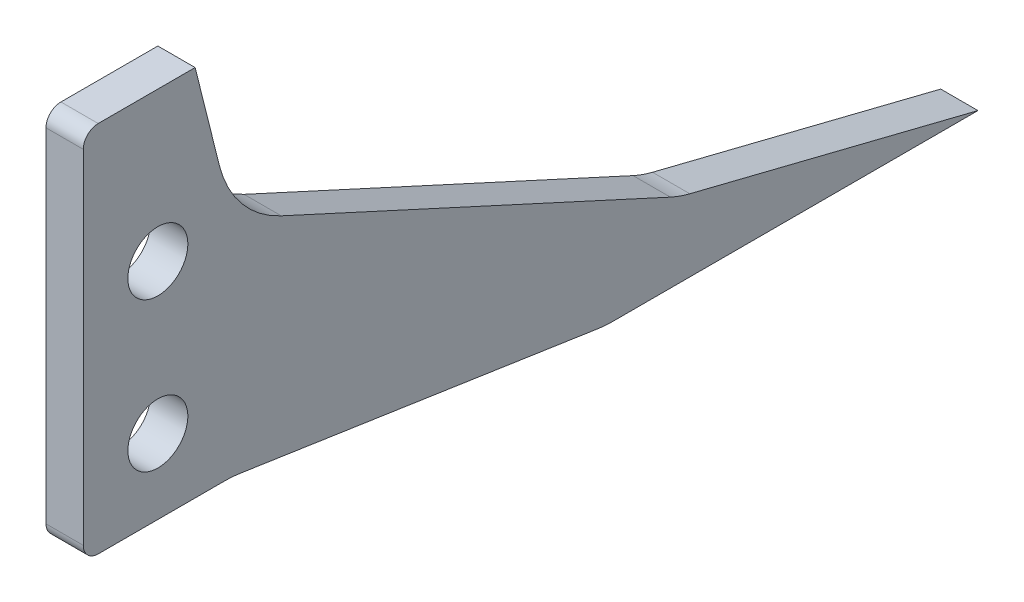
SolidWorks part; units mm, degrees
material "PLA/ABS"
ref_plane "Front Plane" through (0, 0, 0) normal (0, 0, 1) x (1, 0, 0)
ref_plane "Top Plane" through (0, 0, 0) normal (0, 1, 0) x (1, 0, 0)
ref_plane "Right Plane" through (0, 0, 0) normal (1, 0, 0) x (0, 0, -1)
other "Center of Mass"
other "Bounding Box"
ref_plane "Default Plane" through (-8.9266, -12.7485, 0) normal (-0.1736, 0.9848, 0) x (0.9848, 0.1736, 0)
sketch "Sketch1" plane through (0, 0, 0) normal (0, 1, 0) x (1, 0, 0)
  line L0 (0, 0) -> (0, -50.8) construction
  line L1 (0, -50.8) -> (-6.35, -50.8) construction
  line L2 (-63.5, -50.8) -> (-57.15, -50.8) construction
  line L3 (-57.15, -60.7695) -> (-6.35, -60.7695)
  line L4 (-57.15, -60.7695) -> (-57.15, -40.8305)
  line L5 (-57.15, -40.8305) -> (-6.35, -40.8305)
  line L6 (-6.35, -60.7695) -> (-6.35, -40.8305)
  line L7 (-57.15, -60.7695) -> (-6.35, -40.8305) construction
  line L8 (-57.15, -40.8305) -> (-6.35, -60.7695) construction
  line L9 (-73.66, -71.4375) -> (-63.5, -71.4375)
  line L10 (-73.66, -71.4375) -> (-73.66, -30.1625)
  line L11 (-73.66, -30.1625) -> (-63.5, -30.1625)
  line L12 (-63.5, -71.4375) -> (-63.5, -30.1625)
  line L13 (-73.66, -71.4375) -> (-63.5, -30.1625) construction
  line L14 (-73.66, -30.1625) -> (-63.5, -71.4375) construction
  line L15 (57.15, -40.8305) -> (6.35, -40.8305)
  line L16 (-47.625, -82.55) -> (9.525, -82.55)
  line L17 (-47.625, -82.55) -> (-47.625, -66.04)
  line L18 (-47.625, -66.04) -> (9.525, -66.04)
  line L19 (9.525, -82.55) -> (9.525, -66.04)
  line L20 (-47.625, -82.55) -> (9.525, -66.04) construction
  line L21 (-47.625, -66.04) -> (9.525, -82.55) construction
  line L22 (6.35, -60.7695) -> (6.35, -40.8305)
  line L23 (57.15, -60.7695) -> (6.35, -60.7695)
  line L24 (57.15, -60.7695) -> (57.15, -40.8305)
  line L25 (73.66, -30.1625) -> (63.5, -30.1625)
  line L26 (63.5, -71.4375) -> (63.5, -30.1625)
  line L27 (73.66, -71.4375) -> (63.5, -71.4375)
  line L28 (73.66, -71.4375) -> (73.66, -30.1625)
  line L30 (47.625, -82.55) -> (4.445, -82.55)
  line L31 (47.625, -82.55) -> (47.625, -62.4078)
  line L32 (47.625, -62.4078) -> (4.445, -62.4078)
  line L33 (4.445, -82.55) -> (4.445, -62.4078)
  line L34 (47.625, -82.55) -> (4.445, -62.4078) construction
  line L35 (47.625, -62.4078) -> (4.445, -82.55) construction
  line L36 (-57.15, -88.9) -> (57.15, -88.9)
  line L37 (-57.15, -88.9) -> (-57.15, 0)
  line L38 (-57.15, 0) -> (57.15, 0)
  line L39 (57.15, -88.9) -> (57.15, 0)
  line L40 (-57.15, -88.9) -> (57.15, 0) construction
  line L41 (-57.15, 0) -> (57.15, -88.9) construction
  point P3 (-19.05, -74.295)
  point P6 (-31.75, -50.8)
  point P12 (-68.58, -50.8)
  point P22 (0, 0)
  point P23 (0, -44.45)
  point P36 (0, 6.35)
  point P38 (26.035, -72.4789)
  dimension "D2" = 50.8
  dimension "D3" = 19.939
  dimension "D4" = 41.275
  dimension "D5" = 10.16
  dimension "D6" = 57.15
  dimension "D7" = 16.51
  dimension "D8" = 43.18
  dimension "D9" = 20.1422
  dimension "D10" = 6.35
  dimension "D11" = 114.3
  dimension "D12" = 38.1
  dimension "D13" = 6.35
  dimension "D14" = 9.525
  dimension "D15" = 6.35
  dimension "D16" = 9.525
  dimension "D17" = 88.9
  dimension "D18" = 6.35
sketch "Sketch2" plane through (0, 0, 0) normal (1, 0, 0) x (0, 0, -1)
  line L1 (-88.9, 12.7) -> (0, 12.7)
  line L2 (-88.9, 12.7) -> (-88.9, -12.7)
  line L3 (-88.9, -12.7) -> (0, -12.7)
  line L4 (0, 12.7) -> (0, -12.7)
  line L5 (-88.9, 12.7) -> (0, -12.7) construction
  line L6 (-88.9, -12.7) -> (0, 12.7) construction
  line L7 (-88.9, 12.7) -> (12.7, 12.7)
  line L8 (-88.9, 12.7) -> (-88.9, 15.875)
  line L9 (-88.9, 15.875) -> (12.7, 15.875)
  line L10 (12.7, 12.7) -> (12.7, 15.875)
  line L11 (-88.9, 12.7) -> (12.7, 15.875) construction
  line L12 (-88.9, 15.875) -> (12.7, 12.7) construction
  line L13 (-88.9, -12.7) -> (0, -12.7)
  line L14 (-88.9, -12.7) -> (-88.9, -15.875)
  line L15 (-88.9, -15.875) -> (0, -15.875)
  line L16 (0, -12.7) -> (0, -15.875)
  line L17 (-88.9, -12.7) -> (0, -15.875) construction
  line L18 (-88.9, -15.875) -> (0, -12.7) construction
  circle A0 centre (-50.8, 0) radius 20.6375
  point P4 (-71.4375, 0)
  point P5 (-44.45, 0)
  point P15 (-38.1, 14.2875)
  point P19 (-44.45, -14.2875)
  dimension "D1" = 25.4
  dimension "D2" = 3.175
  dimension "D3" = 12.7
sketch "Sketch3" plane through (0, 0, 0) normal (0, 1, 0) x (1, 0, 0)
  line L1 (-57.15, -88.9) -> (57.15, -88.9)
  line L2 (-57.15, -88.9) -> (-57.15, 0)
  line L3 (-57.15, 0) -> (57.15, 0)
  line L4 (57.15, -88.9) -> (57.15, 0)
  line L5 (-57.15, -88.9) -> (57.15, 0) construction
  line L6 (-57.15, 0) -> (57.15, -88.9) construction
  line L7 (-47.625, -6.35) -> (47.625, -6.35)
  line L8 (-47.625, -6.35) -> (-47.625, -82.55)
  line L9 (-47.625, -82.55) -> (47.625, -82.55)
  line L10 (47.625, -6.35) -> (47.625, -82.55)
  line L11 (-47.625, -6.35) -> (47.625, -82.55) construction
  line L12 (-47.625, -82.55) -> (47.625, -6.35) construction
  point P0 (0, -44.45)
  point P7 (0, -44.45)
extrude "Boss-Extrude1" add sketch "Sketch3" along normal up to vertex (12.7 mm away) and the other way up to vertex (12.7 mm away) up to point (0, 12.7, 88.9) other way up to point (0, -12.7, 88.9)
sketch "Sketch4" plane through (0, -12.7, 0) normal (0, -1, 0) x (1, 0, 0)
  line L1 (-57.15, 88.9) -> (57.15, 88.9)
  line L2 (-57.15, 88.9) -> (-57.15, 0)
  line L3 (-57.15, 0) -> (57.15, 0)
  line L4 (57.15, 88.9) -> (57.15, 0)
  line L5 (-57.15, 88.9) -> (57.15, 0) construction
  line L6 (-57.15, 0) -> (57.15, 88.9) construction
  point P0 (0, 44.45)
extrude "Boss-Extrude2" add sketch "Sketch4" along normal up to vertex (3.175 mm away) up to point (0, -15.875, 88.9)
sketch "Sketch5" plane through (0, 12.7, 0) normal (0, 1, 0) x (1, 0, 0)
  line L1 (-57.15, 0) -> (-57.15, -88.9)
  line L2 (-57.15, -88.9) -> (57.15, -88.9)
  line L3 (57.15, -88.9) -> (57.15, 0)
  line L5 (-57.15, 0) -> (57.15, 0)
extrude "Boss-Extrude3" add sketch "Sketch5" along normal up to vertex (3.175 mm away) separate body up to point (0, 15.875, 88.9)
sketch "Sketch7" plane through (0, -12.7, 0) normal (0, 1, 0) x (1, 0, 0)
  line L0 (-6.35, -60.7695) -> (-6.35, -40.8305) construction
  line L1 (-47.625, -38.1) -> (-6.35, -38.1)
  line L2 (-47.625, -38.1) -> (-47.625, -63.5)
  line L3 (-47.625, -63.5) -> (-6.35, -63.5)
  line L4 (-6.35, -38.1) -> (-6.35, -63.5)
  line L5 (-47.625, -38.1) -> (-6.35, -63.5) construction
  line L6 (-47.625, -63.5) -> (-6.35, -38.1) construction
  line L7 (47.625, -38.1) -> (6.35, -38.1)
  line L8 (47.625, -38.1) -> (47.625, -63.5)
  line L9 (47.625, -63.5) -> (6.35, -63.5)
  line L10 (6.35, -38.1) -> (6.35, -63.5)
  line L11 (47.625, -38.1) -> (6.35, -63.5) construction
  line L12 (47.625, -63.5) -> (6.35, -38.1) construction
  line L13 (6.35, -60.7695) -> (6.35, -40.8305) construction
  line L14 (0, -50.8) -> (-6.35, -50.8) construction
  line L15 (47.625, -82.55) -> (47.625, -6.35) construction
  line L16 (-47.625, -6.35) -> (-47.625, -82.55) construction
  point P4 (-26.9875, -50.8)
  point P10 (26.9875, -50.8)
  dimension "D1" = 25.4
extrude "Boss-Extrude4" add sketch "Sketch7" along normal blind 6.35
sketch "Sketch6" plane through (-57.15, 0, 0) normal (-1, 0, 0) x (0, 0, 1)
  circle A0 centre (50.8, 0) radius 9.9695
extrude "Cut-Extrude1" cut sketch "Sketch6" against normal through all
ref_plane "Plane1" through (0, 0, 0) normal (1, 0, 0) x (0, 0, -1)
sketch "Sketch13" plane through (0, -12.7, 0) normal (0, 1, 0) x (1, 0, 0)
  line L0 (-47.625, -63.5) -> (-6.35, -63.5) construction
  line L1 (-6.35, -38.1) -> (-32.385, -38.1)
  line L2 (-6.35, -38.1) -> (-6.35, -63.5)
  line L3 (-6.35, -63.5) -> (-32.385, -63.5)
  line L4 (-32.385, -38.1) -> (-32.385, -63.5)
  line L5 (-6.35, -38.1) -> (-32.385, -63.5) construction
  line L6 (-6.35, -63.5) -> (-32.385, -38.1) construction
  line L7 (-47.625, -38.1) -> (-47.625, -43.1144) construction
  line L9 (0, -20.0819) -> (0, 20.0819) construction
  line L10 (32.385, -38.1) -> (32.385, -63.5)
  line L11 (6.35, -63.5) -> (32.385, -63.5)
  line L12 (6.35, -38.1) -> (6.35, -63.5)
  line L13 (6.35, -38.1) -> (32.385, -38.1)
  point P4 (-19.3675, -50.8)
  dimension "D1" = 15.24
extrude "Boss-Extrude5" add sketch "Sketch13" along normal blind 4.064
sketch "Sketch19" plane through (0, 12.7, 0) normal (0, 1, 0) x (1, 0, 0)
  line L0 (-57.15, 0) -> (-57.15, -88.9) construction
  line L1 (57.15, 0) -> (-57.15, 0) construction
  line L5 (57.15, -88.9) -> (57.15, 0) construction
  line L6 (57.15, 0) -> (-57.15, 0) construction
  line L7 (-57.15, -88.9) -> (57.15, -88.9) construction
  line L8 (-47.625, -82.55) -> (47.625, -82.55) construction
  circle A0 centre (-53.975, -3.175) radius 3.175 construction
  circle A1 centre (-53.975, -3.175) radius 0.9525
  circle A2 centre (53.975, -3.175) radius 3.175 construction
  circle A3 centre (53.975, -3.175) radius 0.9525
  circle A4 centre (-53.975, -85.725) radius 3.175 construction
  circle A5 centre (-53.975, -85.725) radius 0.9525
  circle A6 centre (53.975, -85.725) radius 3.175 construction
  circle A7 centre (53.975, -85.725) radius 0.9525
  dimension "D1" = 1.905
  dimension "D2" = 6.35
extrude "Cut-Extrude4" cut sketch "Sketch19" against normal blind 25.4
sketch "Sketch20" plane through (0, 15.875, 0) normal (0, 1, 0) x (1, 0, 0)
  circle A0 centre (-53.975, -3.175) radius 1.905
  circle A1 centre (-53.975, -85.725) radius 1.905
  circle A2 centre (53.975, -85.725) radius 1.905
  circle A3 centre (53.975, -3.175) radius 1.905
  dimension "D1" = 3.81
  dimension "D2" = 3.81
  dimension "D3" = 3.81
  dimension "D4" = 3.81
extrude "Cut-Extrude7" cut sketch "Sketch20" against normal up to surface (3.175 mm away) up to face at (0, 12.7, 44.45)
sketch "Sketch23" plane through (0, 15.875, 0) normal (0, 1, 0) x (1, 0, 0)
  line L0 (-57.15, -88.9) -> (57.15, -88.9) construction
  line L1 (44.45, -62.8085) -> (28.015, -62.8085) construction
  line L2 (44.45, -62.8085) -> (44.45, -76.2) construction
  line L3 (44.45, -76.2) -> (28.015, -76.2) construction
  line L4 (28.015, -62.8085) -> (28.015, -76.2) construction
  line L5 (44.45, -62.8085) -> (28.015, -76.2) construction
  line L6 (44.45, -76.2) -> (28.015, -62.8085) construction
  line L7 (57.15, -88.9) -> (57.15, 0) construction
  circle A0 centre (36.2325, -69.5043) radius 5.08
  circle A1 centre (44.45, -62.8085) radius 1.905
  circle A2 centre (28.015, -76.2) radius 1.905
  circle A4 centre (2.615, -60.4273) radius 2.3812
  point P0 (36.2325, -69.5043)
  dimension "D1" = 10.16
  dimension "D2" = 3.81
  dimension "D3" = 10.6
  dimension "D4" = 12.7
  dimension "D7" = 4.7625
  dimension "D8" = 25.4
  dimension "D5" = 12.7
  dimension "D6" = 13.3915
extrude "Cut-Extrude8" cut sketch "Sketch23" against normal up to surface (3.175 mm away) up to face at (53.975, 12.7, 5.08)
sketch "Sketch25" plane through (0, 0, 0) normal (1, 0, 0) x (0, 0, -1)
  line L0 (0, -15.875) -> (0, 15.875)
  line L1 (0, 15.875) -> (9.525, 15.875)
  line L2 (9.525, 15.875) -> (12.7, 3.175)
  line L3 (12.7, 3.175) -> (12.7, -15.875)
  line L4 (12.7, -15.875) -> (0, -15.875)
  dimension "D1" = 12.7
  dimension "D2" = 9.525
  dimension "D3" = 19.05
extrude "Boss-Extrude6" add sketch "Sketch25" along normal mid plane 50.8
sketch "Sketch26" plane through (25.4, 0, 0) normal (1, 0, 0) x (0, 0, -1)
  line L0 (-91.2367, -20.6375) -> (2.1353, -20.6375) construction
  line L1 (0, 15.875) -> (9.525, 15.875)
  line L2 (9.525, 15.875) -> (12.7, 3.175)
  line L3 (12.7, 3.175) -> (50.8, -14.2875)
  line L4 (76.2, -20.6375) -> (44.45, -20.6375)
  line L5 (44.45, -20.6375) -> (12.7, -15.875)
  line L6 (12.7, -15.875) -> (0, -15.875)
  line L7 (0, -15.875) -> (0, 15.875)
  line L8 (12.7, -15.875) -> (12.7, 3.175) construction
  line L10 (76.2, -20.6375) -> (50.8, -14.2875)
  circle A0 centre (-50.8, 0) radius 20.6375 construction
  dimension "D1" = 63.5
  dimension "D2" = 31.75
  dimension "D3" = 6.35
  dimension "D4" = 25.4
extrude "Boss-Extrude7" add sketch "Sketch26" along normal blind 3.175 separate body
sketch "Sketch27" plane through (25.4, 0, 0) normal (1, 0, 0) x (0, 0, -1)
  line L0 (0, -9.525) -> (6.35, -9.525) construction
  line L1 (0, 12.7) -> (0, -12.7) construction
  line L2 (6.35, -9.525) -> (12.7, -9.525) construction
  line L4 (12.7, -15.875) -> (12.7, 3.175) construction
  line L5 (6.35, -9.525) -> (6.35, 3.175) construction
  line L6 (0, -15.875) -> (12.7, -15.875) construction
  circle A0 centre (6.35, -9.525) radius 4.7625
  circle A1 centre (6.35, 3.175) radius 4.7625
  dimension "D1" = 9.525
  dimension "D2" = 6.35
  dimension "D3" = 12.7
extrude "Cut-Extrude9" cut sketch "Sketch27" against normal through all and the other way through all
sketch "Sketch28" plane through (25.4, 0, 0) normal (-1, 0, 0) x (0, 0, 1)
  circle A0 centre (-6.35, 3.175) radius 2.5527
  circle A1 centre (-6.35, -9.525) radius 2.5527
  dimension "D1" = 5.1054
extrude "Cut-Extrude10" cut sketch "Sketch28" against normal through all
fillet "Fillet1" radius 9.525 4 edges at (26.9875, -15.875, -12.7) (26.9875, -20.6375, -44.45) (26.9875, -14.2875, -50.8) (26.9875, 3.175, -12.7)
fillet "Fillet2" radius 1.27 2 edges at (26.9875, -15.875, 0) (26.9875, 15.875, 0)
mirror "Mirror1" about plane through (0, 0, 0) normal (1, 0, 0) of bodies 123 120
sketch "Sketch29" plane through (0, 0, 38.1) normal (0, 0, -1) x (-1, 0, 0)
  line L0 (-47.625, -12.7) -> (-6.35, -12.7) construction
  line L1 (-29.5275, -10.16) -> (-23.1775, -10.16)
  line L2 (-29.5275, -10.16) -> (-29.5275, -15.24)
  line L3 (-29.5275, -15.24) -> (-23.1775, -15.24)
  line L4 (-23.1775, -10.16) -> (-23.1775, -15.24)
  line L5 (-29.5275, -10.16) -> (-23.1775, -15.24) construction
  line L6 (-29.5275, -15.24) -> (-23.1775, -10.16) construction
  line L7 (-32.385, -8.636) -> (-6.35, -8.636) construction
  line L8 (-15.5575, -10.16) -> (-9.2075, -10.16)
  line L9 (-15.5575, -10.16) -> (-15.5575, -15.24)
  line L10 (-15.5575, -15.24) -> (-9.2075, -15.24)
  line L11 (-9.2075, -10.16) -> (-9.2075, -15.24)
  line L12 (-15.5575, -10.16) -> (-9.2075, -15.24) construction
  line L13 (-15.5575, -15.24) -> (-9.2075, -10.16) construction
  line L14 (-32.385, -8.636) -> (-6.35, -8.636) construction
  line L15 (-32.385, -8.636) -> (-32.385, -12.7) construction
  line L16 (-32.385, -12.7) -> (-29.5275, -12.7) construction
  line L17 (-6.35, -8.636) -> (-6.35, -12.7) construction
  line L18 (-6.35, -12.7) -> (-9.2075, -12.7) construction
  point P0 (-26.3525, -12.7)
  point P7 (-12.3825, -12.7)
  dimension "D1" = 6.35
  dimension "D2" = 7.62
  dimension "D3" = 5.08
extrude "Cut-Extrude11" cut sketch "Sketch29" against normal offset from surface 6.35 and the other way blind 6.35 up to face at (26.9875, -9.525, 63.5) offset beyond the face yes
mirror "Mirror2" about plane through (0, 0, 0) normal (1, 0, 0) of "Cut-Extrude11"
delete or keep bodies "Body-Delete/Keep 1" [suppressed] type keep bodies bodies 116
delete or keep bodies "Body-Delete/Keep 2" type keep bodies bodies 123
delete or keep bodies "Body-Delete/Keep 3" [suppressed] type keep bodies bodies 125
